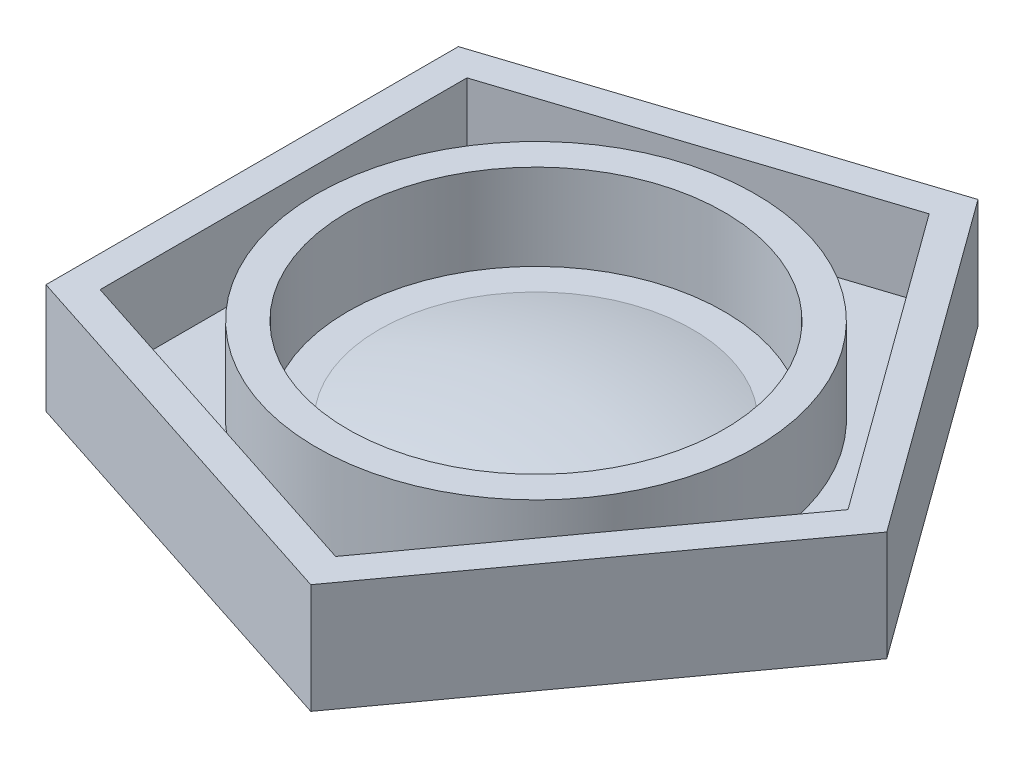
SolidWorks part; units mm, degrees
ref_plane "Front Plane" through (0, 0, 0) normal (0, 0, 1) x (1, 0, 0)
ref_plane "Top Plane" through (0, 0, 0) normal (0, 1, 0) x (1, 0, 0)
ref_plane "Right Plane" through (0, 0, 0) normal (1, 0, 0) x (0, 0, -1)
sketch "Sketch1" plane through (0, 0, 0) normal (0, 0, 1) x (1, 0, 0)
  line L0 (15.24, -15.4939) -> (12.7, -15.4939)
  line L1 (-12.7, -15.4939) -> (-15.24, -15.4939)
  line L2 (0, -13.8808) -> (0, -18.0339)
  line L3 (15.24, -15.4939) -> (12.7, -15.4939)
  line L4 (-15.24, -15.4939) -> (-15.24, -8.5287)
  line L5 (15.24, -8.5287) -> (15.24, -15.4939)
  line L6 (15.24, -8.5287) -> (15.24, -15.4939)
  line L7 (0, -18.0339) -> (17.78, -18.0339)
  line L8 (0, -13.8808) -> (0, -8.5287) construction
  line L9 (0, -8.5287) -> (15.24, -8.5287) construction
  line L10 (17.78, -18.0339) -> (17.78, -8.5287)
  line L11 (17.78, -8.5287) -> (15.24, -8.5287)
  arc A0 (12.7, -15.4939) -> (-12.7, -15.4939) centre (0, -64.6808) ccw
  arc A1 (12.7, -15.4939) -> (0, -13.8808) centre (0, -64.6808) ccw
  dimension "D1" = 2.54
  dimension "D2" = 2.54
revolve "Revolve1" add sketch "Sketch1" angle 360 about L2
sketch "Sketch2" plane through (0, -18.0339, 0) normal (0, -1, 0) x (1, 0, 0)
  line L0 (23.6518, 2.0165) -> (9.2266, 21.8711) construction
  line L1 (28.4135, 0) -> (8.7803, 27.0228)
  line L2 (8.7803, 27.0228) -> (-22.987, 16.701)
  line L3 (-22.987, 16.701) -> (-22.987, -16.701)
  line L4 (-22.987, -16.701) -> (8.7803, -27.0228)
  line L5 (8.7803, -27.0228) -> (28.4135, 0)
  circle A0 centre (0, 0) radius 22.987 construction
  dimension "D1" = 2.667
extrude "Boss-Extrude1" add sketch "Sketch2" against normal up to surface (2.54 mm away)
sketch "Sketch3" plane through (0, -15.4939, 0) normal (0, 1, 0) x (1, 0, 0)
  line L0 (25.2739, 0) -> (7.8101, 24.0369)
  line L1 (7.8101, 24.0369) -> (-20.447, 14.8556)
  line L2 (-20.447, 14.8556) -> (-20.447, -14.8556)
  line L3 (-20.447, -14.8556) -> (7.8101, -24.0369)
  line L4 (7.8101, -24.0369) -> (25.2739, 0)
  line L5 (28.4135, 0) -> (8.7803, 27.0228)
  line L6 (8.7803, 27.0228) -> (-22.987, 16.701)
  line L7 (-22.987, 16.701) -> (-22.987, -16.701)
  line L8 (-22.987, -16.701) -> (8.7803, -27.0228)
  line L9 (8.7803, -27.0228) -> (28.4135, 0)
  line L10 (28.4135, 0) -> (8.7803, 27.0228)
  line L11 (8.7803, 27.0228) -> (-22.987, 16.701)
  line L12 (-22.987, 16.701) -> (-22.987, -16.701)
  line L13 (-22.987, -16.701) -> (8.7803, -27.0228)
  line L14 (8.7803, -27.0228) -> (28.4135, 0)
  dimension "D1" = 0
  dimension "D2" = 2.54
extrude "Boss-Extrude2" add sketch "Sketch3" along normal blind 6.35
